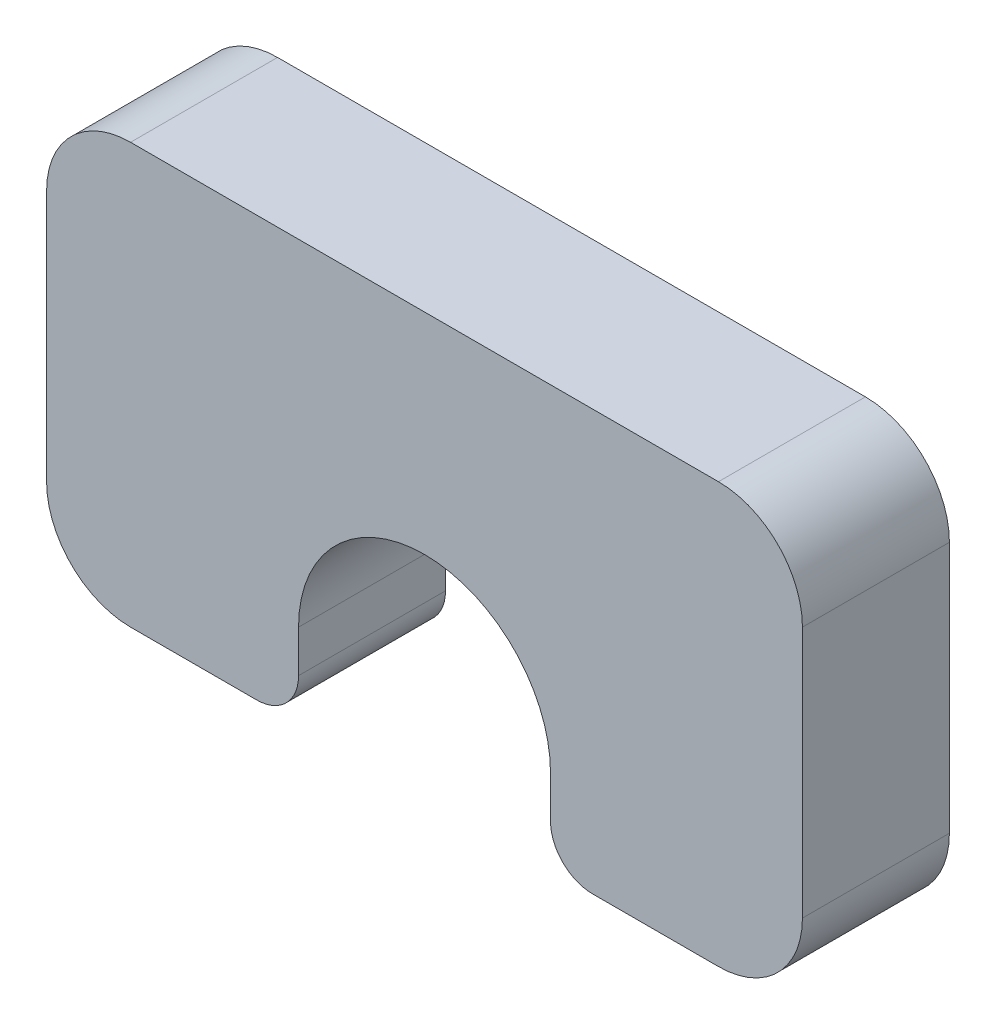
SolidWorks part; units mm, degrees
material "Plain Carbon Steel"
ref_plane "Front Plane" through (0, 0, 0) normal (0, 0, 1) x (1, 0, 0)
ref_plane "Top Plane" through (0, 0, 0) normal (0, 1, 0) x (1, 0, 0)
ref_plane "Right Plane" through (0, 0, 0) normal (1, 0, 0) x (0, 0, -1)
sketch "Sketch1" plane through (0, 0, 0) normal (0, 0, 1) x (1, 0, 0)
  line L1 (2, 0) -> (5, 0)
  line L2 (0, 2) -> (0, 8)
  line L3 (2, 10) -> (16, 10)
  line L4 (18, 2) -> (18, 8)
  line L5 (6, 1) -> (6, 2)
  line L6 (12, 1) -> (12, 2)
  line L7 (13, 0) -> (16, 0)
  arc A1 (12, 2) -> (6, 2) centre (9, 2) ccw
  arc A2 (12, 1) -> (13, 0) centre (13, 1) ccw
  arc A3 (6, 1) -> (5, 0) centre (5, 1) cw
  arc A4 (2, 0) -> (0, 2) centre (2, 2) cw
  arc A5 (16, 0) -> (18, 2) centre (16, 2) ccw
  arc A6 (16, 10) -> (18, 8) centre (16, 8) cw
  arc A7 (0, 8) -> (2, 10) centre (2, 8) cw
  point P7 (9, 1)
  point P19 (0, 0)
  point P24 (18, 10)
  point P27 (0, 10)
  dimension "D4" = 3
  dimension "D3" = 1
  dimension "D5" = 1
  dimension "D7" = 9
  dimension "D8" = 5
  dimension "D9" = 13
  dimension "D12" = 2
  dimension "D13" = 2
  dimension "D14" = 2
  dimension "D15" = 2
  dimension "D1" = 18
  dimension "D2" = 10
  dimension "D6" = 2
  dimension "D10" = 1
  dimension "D11" = 1
extrude "Boss-Extrude1" add sketch "Sketch1" along normal mid plane 3.5
